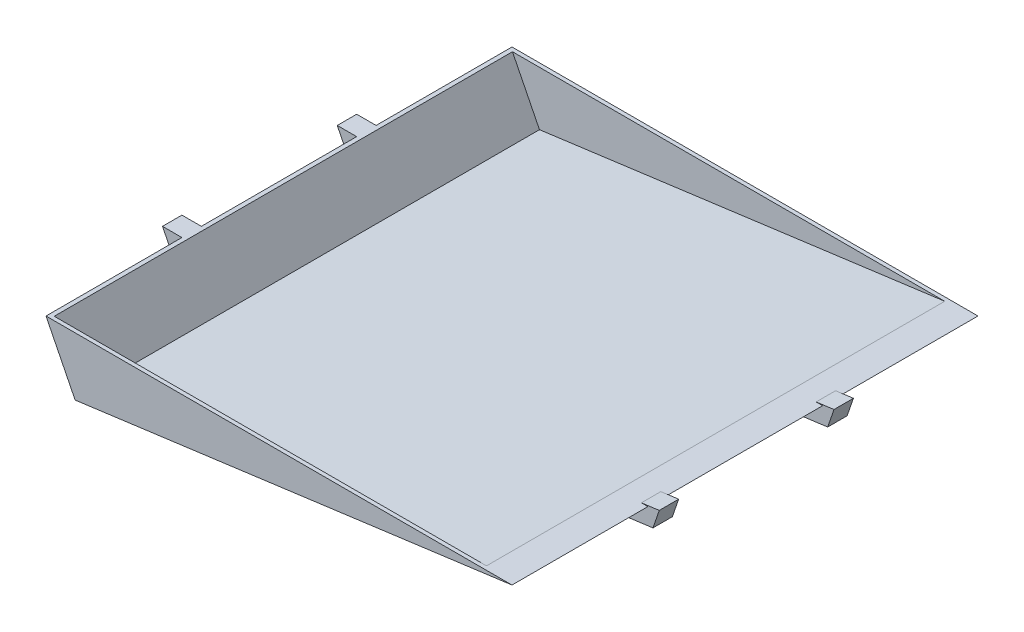
SolidWorks part; units mm, degrees
ref_plane "Front Plane" through (0, 0, 0) normal (0, 0, 1) x (1, 0, 0)
ref_plane "Top Plane" through (0, 0, 0) normal (0, 1, 0) x (1, 0, 0)
ref_plane "Right Plane" through (0, 0, 0) normal (1, 0, 0) x (0, 0, -1)
sketch3d "3DSketch1"
  line L2 (574.7508, 1402.4171, 1756.2546) -> (612.8508, 1326.2171, 1756.2546)
  line L3 (612.8508, 1326.2171, 1756.2546) -> (1184.3508, 1402.4171, 1756.2546)
  line L4 (1184.3508, 1402.4171, 1756.2546) -> (574.7508, 1402.4171, 1756.2546)
extrude "Boss-Extrude1" add sketch "3DSketch1" along a picked direction on the side of the normal blind 609.6 contours L2 L3 L4
shell "Shell1" thickness 5.08
sketch "Sketch1" plane through (0, 1402.4171, 0) normal (0, 1, 0) x (1, 0, 0)
  line L0 (562.0508, -1756.2546) -> (562.0508, -1146.6546) construction
  line L1 (1184.3508, -1756.2546) -> (574.7508, -1756.2546) construction
  line L2 (1184.3508, -1146.6546) -> (574.7508, -1146.6546) construction
  line L3 (574.7508, -1756.2546) -> (574.7508, -1146.6546) construction
  line L5 (574.7508, -1553.0546) -> (549.3508, -1553.0546)
  line L6 (574.7508, -1553.0546) -> (574.7508, -1578.4546)
  line L7 (574.7508, -1578.4546) -> (549.3508, -1578.4546)
  line L8 (549.3508, -1553.0546) -> (549.3508, -1578.4546)
  line L9 (574.7508, -1553.0546) -> (549.3508, -1578.4546) construction
  line L10 (574.7508, -1578.4546) -> (549.3508, -1553.0546) construction
  point P8 (562.0508, -1565.7546)
  dimension "D1" = 0
  dimension "D2" = 0
  dimension "D3" = 12.7
  dimension "D4" = 0
  dimension "D5" = 190.5
  dimension "D7" = 25.4
ref_plane "Plane1" through (0, 0, 1565.7546) normal (0, 0, 1) x (1, 0, 0)
sketch "Sketch3" plane through (0, 0, 1565.7546) normal (0, 0, 1) x (1, 0, 0)
  line L0 (562.0508, 1402.4171) -> (605.7838, 1314.9511)
  line L1 (574.7508, 1402.4171) -> (612.8508, 1326.2171) construction
  line L3 (605.7838, 1314.9511) -> (1195.0638, 1393.5217)
  line L4 (612.8508, 1326.2171) -> (1184.3508, 1402.4171) construction
  dimension "D1" = 97.79
  dimension "D2" = 0
  dimension "D3" = 589.28
  dimension "D4" = 0
sweep "Sweep1" add profiles "Sketch1" path "Sketch3"
ref_plane "Plane2" through (0, 0, 1451.4546) normal (0, 0, 1) x (1, 0, 0)
mirror "Mirror1" about plane through (0, 0, 1451.4546) normal (0, 0, 1) of "Sweep1"
sketch "Sketch4" plane through (0, 0, 1553.0546) normal (0, 0, -1) x (-1, 0, 0)
  line L0 (-599.2493, 1302.6201) -> (-624.6493, 1306.0067)
  line L1 (-599.2493, 1302.6201) -> (-1190.9353, 1381.5115) construction
  line L2 (-599.2493, 1302.6201) -> (-587.8901, 1325.3385)
  line L3 (-549.3508, 1402.4171) -> (-599.2493, 1302.6201) construction
  line L4 (-624.6493, 1306.0067) -> (-612.8508, 1326.2171)
  line L5 (-612.8508, 1326.2171) -> (-587.8901, 1325.3385)
  dimension "D1" = 25.4
  dimension "D2" = 25.4
extrude "Boss-Extrude5" add sketch "Sketch4" along normal blind 203.2 separate body
